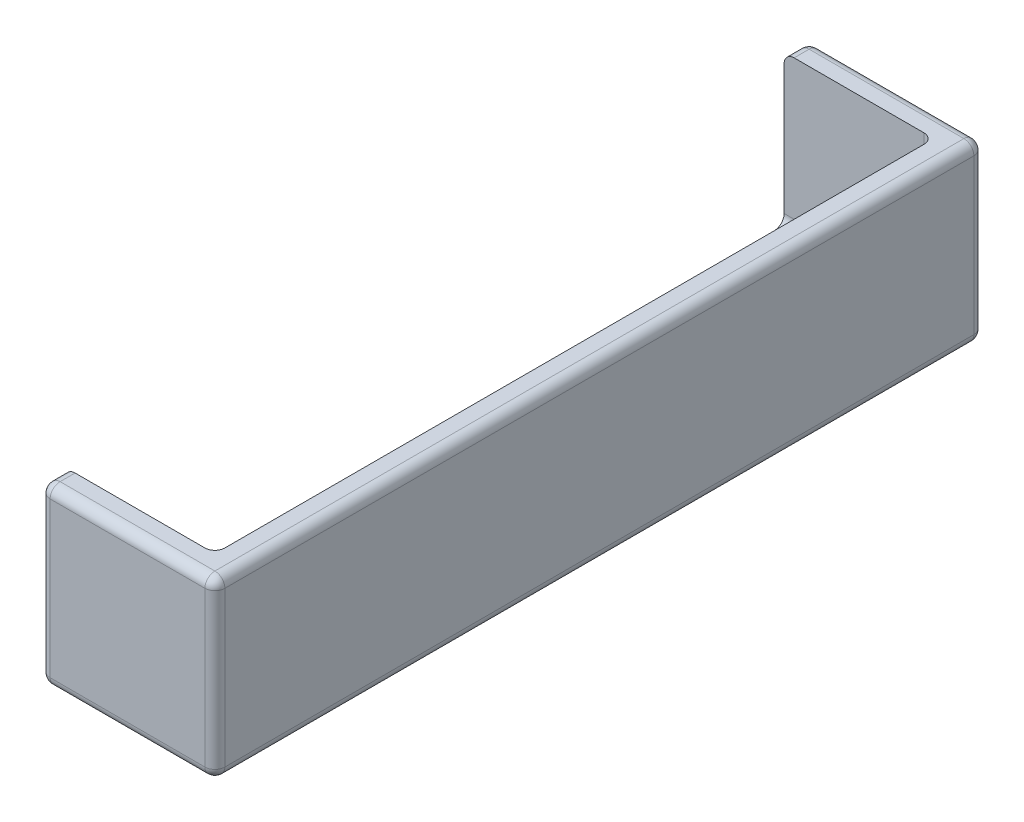
SolidWorks part; units mm, degrees
ref_plane "Plan de face" through (0, 0, 0) normal (0, 0, 1) x (1, 0, 0)
ref_plane "Plan de dessus" through (0, 0, 0) normal (0, 1, 0) x (1, 0, 0)
ref_plane "Plan de droite" through (0, 0, 0) normal (1, 0, 0) x (0, 0, -1)
sketch "Esquisse1" plane through (0, 0, 0) normal (0, 0, 1) x (1, 0, 0)
  line L1 (0, 0) -> (0, 17.5)
  line L2 (0, 17.5) -> (17.5, 17.5)
  line L3 (17.5, 17.5) -> (17.5, 0)
  line L4 (17.5, 0) -> (0, 0)
  point P0 (0, 0)
  dimension "D1" = 17.5
  dimension "D2" = 17.5
extrude "Boss.-Extru.1" add sketch "Esquisse1" along normal blind 77 contours L1 L2 L3 L4
sketch "Esquisse2" plane through (0, 0, 0) normal (-1, 0, 0) x (0, 0, 1)
  line L0 (0, 0) -> (0, 17.5) construction
  line L1 (2.5, 22.5) -> (74.5, 22.5)
  line L2 (2.5, 22.5) -> (2.5, 2.5)
  line L3 (2.5, 2.5) -> (74.5, 2.5)
  line L4 (74.5, 22.5) -> (74.5, 2.5)
  line L5 (77, 0) -> (77, 17.5) construction
  line L6 (77, 0) -> (0, 0) construction
  line L7 (77, 17.5) -> (0, 17.5) construction
  dimension "D1" = 2.5
  dimension "D2" = 2.5
  dimension "D3" = 2.5
  dimension "D4" = 5
extrude "Enlèv. mat.-Extru.1" cut sketch "Esquisse2" against normal blind 15
fillet "Congé1" radius 1 18 edges at (17.5, 8.75, 77) (8.75, 0, 77) (17.5, 0, 38.5) (17.5, 8.75, 0) (8.75, 0, 0) (15, 2.5, 38.5) (7.5, 2.5, 74.5) (15, 10, 74.5) (7.5, 2.5, 2.5) (15, 10, 2.5) (8.75, 17.5, 0) (0, 8.75, 0) (0, 0, 38.5) (17.5, 17.5, 38.5) (0, 17.5, 1.25) (0, 17.5, 75.75) (0, 8.75, 77) (8.75, 17.5, 77)
equation "\"74.5.00mm\"=73"
